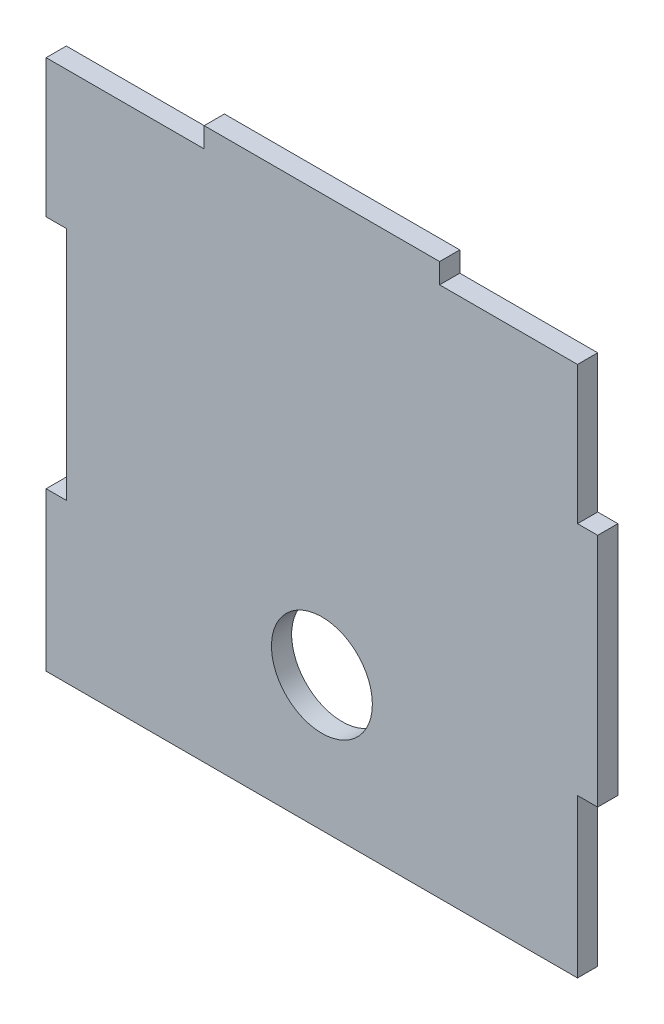
SolidWorks part; units mm, degrees
ref_plane "Front Plane" through (0, 0, 0) normal (0, 0, 1) x (1, 0, 0)
ref_plane "Top Plane" through (0, 0, 0) normal (0, 1, 0) x (1, 0, 0)
ref_plane "Right Plane" through (0, 0, 0) normal (1, 0, 0) x (0, 0, -1)
sketch "Sketch1" plane through (0, 0, 0) normal (0, 0, 1) x (1, 0, 0)
  line L0 (0, 38) -> (0, -39.5) construction
  line L5 (-38, 39.5) -> (-17.5, 39.5)
  line L6 (-38, 16) -> (-38, -16)
  line L24 (38, 39.5) -> (38, 19)
  line L26 (-41, -39.5) -> (38, -39.5)
  line L27 (-38, 0) -> (38, 0) construction
  line L28 (-17.5, 39.5) -> (-17.5, 42.5)
  line L29 (-17.5, 42.5) -> (17.5, 42.5)
  line L30 (17.5, 42.5) -> (17.5, 39.5)
  line L33 (-41, 19) -> (-41, 39.5)
  line L34 (-41, 39.5) -> (-38, 39.5)
  line L35 (-41, -19) -> (-41, -39.5)
  line L36 (38, -19) -> (38, -39.5)
  line L43 (41, 16) -> (41, -16)
  line L44 (-38, 16) -> (-38, 19)
  line L46 (17.5, 39.5) -> (38, 39.5)
  line L48 (-38, 19) -> (-41, 19)
  line L50 (-41, -19) -> (-41, -16)
  line L51 (-41, -16) -> (-38, -16)
  line L52 (38, -19) -> (38, -16)
  line L53 (38, -16) -> (41, -16)
  line L54 (41, 16) -> (41, 19)
  line L55 (41, 19) -> (38, 19)
  point P0 (0, 0)
  dimension "D1" = 79
  dimension "D2" = 76
  dimension "D3" = 3
  dimension "D4" = 35
  dimension "D5" = 3
  dimension "D6" = 76
  dimension "D7" = 35
  dimension "D8" = 3
  dimension "D9" = 3
  dimension "D10" = 3
  dimension "D11" = 3
  dimension "D12" = 35
  dimension "D13" = 0
  dimension "D14" = 20.5
extrude "Boss-Extrude1" add sketch "Sketch1" along normal blind 3
sketch "Sketch2" plane through (0, 0, 3) normal (0, 0, 1) x (1, 0, 0)
  line L9 (-41, -39.5) -> (38, -39.5) construction
  circle A0 centre (0, -19.5) radius 7.5
  dimension "D1" = 15
  dimension "D2" = 20
extrude "Cut-Extrude1" cut sketch "Sketch2" against normal blind 3
